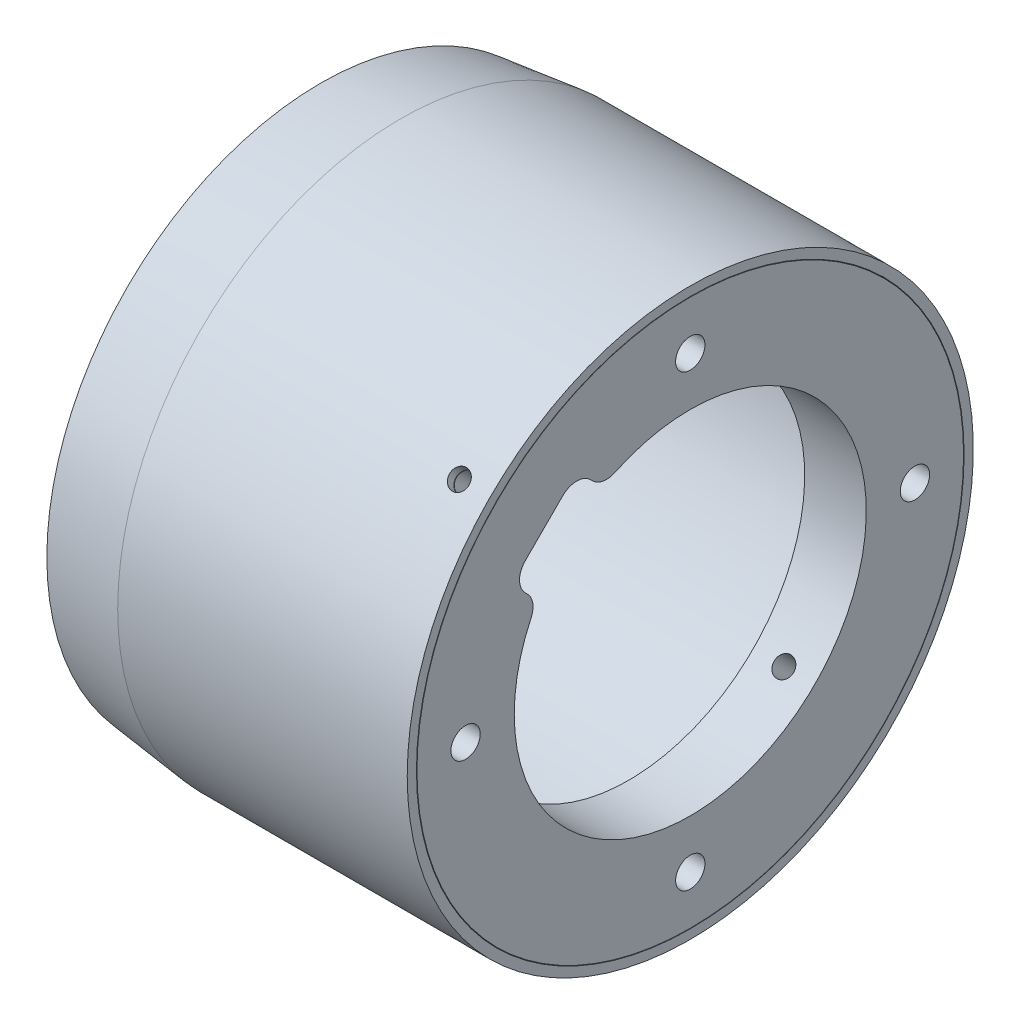
SolidWorks part; units mm, degrees
material "6061 Alloy"
ref_plane "Front Plane" through (0, 0, 0) normal (0, 0, 1) x (1, 0, 0)
ref_plane "Top Plane" through (0, 0, 0) normal (0, 1, 0) x (1, 0, 0)
ref_plane "Right Plane" through (0, 0, 0) normal (1, 0, 0) x (0, 0, -1)
sketch "Sketch1" plane through (0, 0, 0) normal (0, 0, 1) x (1, 0, 0)
  line L0 (0, 0) -> (74.8253, 0) construction
  line L1 (13, 45.95) -> (60, 45.95)
  line L5 (60, 44.45) -> (0, 44.45)
  line L6 (0, 44.45) -> (13, 45.95)
  line L7 (0, 0) -> (0, 44.45) construction
  line L17 (60, 44.45) -> (60, 45.95)
  dimension "D1" = 88.9
  dimension "D2" = 60
  dimension "D3" = 13
  dimension "D6" = 1.5
revolve "Revolve1" add sketch "Sketch1" angle 360 about L0
sketch "Sketch2" plane through (0, 0, 0) normal (0, 0, 1) x (1, 0, 0)
  line L0 (0, 0) -> (60, 0) construction
  line L2 (60, -45.95) -> (60, 45.95) construction
  line L3 (60, 44.37) -> (50, 44.37)
  line L4 (60, 44.37) -> (60, 28.575)
  line L5 (60, 28.575) -> (50, 28.575)
  line L6 (50, 44.37) -> (50, 28.575)
  line L7 (60, -45.95) -> (60, 45.95) construction
  line L8 (60, 44.45) -> (0, 44.45) construction
  dimension "D1" = 10
  dimension "D2" = 28.575
  dimension "D3" = 0.08
revolve "Revolve2" add sketch "Sketch2" angle 360 about L0
sketch "Sketch3" plane through (60, 0, 0) normal (1, 0, 0) x (0, 0, -1)
  line L0 (-36.4725, 0) -> (0, 0) construction
  line L1 (0, 36.4725) -> (0, 0) construction
  line L2 (36.4725, 0) -> (0, 0) construction
  line L3 (0, -36.4725) -> (0, 0) construction
  line L4 (-28.575, 0) -> (-44.37, 0) construction
  circle A0 centre (-36.4725, 0) radius 2.3812
  circle A1 centre (0, 36.4725) radius 2.3812
  circle A2 centre (36.4725, 0) radius 2.3812
  circle A3 centre (0, -36.4725) radius 2.3812
  circle A4 centre (0, 0) radius 28.575 construction
  circle A5 centre (0, 0) radius 44.37 construction
  point P13 (0, 0)
  point P17 (0, 0)
  dimension "D1" = 4.7625
  dimension "D3" = 4
extrude "Cut-Extrude1" cut sketch "Sketch3" against normal through all
ref_plane "Plane1" through (0, 32.4916, 32.4916) normal (0, 0.7071, 0.7071) x (-1, 0, 0)
sketch "Sketch4" plane through (0, 32.4916, 32.4916) normal (0, 0.7071, 0.7071) x (-1, 0, 0)
  line L0 (-55, 0) -> (0, 0) construction
  line L1 (-60, 45.95) -> (-60, -45.95) construction
  circle A0 centre (-55, 0) radius 1.5875
  dimension "D1" = 3.175
  dimension "D2" = 5
extrude "Cut-Extrude2" cut sketch "Sketch4" against normal up to surface (17.4191 mm away)
ref_axis "Axis1" through (60, 0, 0) along (-1, 0, 0)
pattern_circular "CirPattern1" count 4 over 360 about axis through (60, 0, 0) along (-1, 0, 0) of "Cut-Extrude2"
sketch "Sketch5" plane through (60, 0, 0) normal (1, 0, 0) x (0, 0, -1)
  line L0 (0, 0) -> (-20.2056, 20.2056) construction
  line L3 (0, 0) -> (0, 36.4725) construction
  line L5 (-21.9733, 11.3667) -> (-18.4378, 29.0444) construction
  line L6 (-29.0444, 18.4378) -> (-11.3667, 21.9733) construction
  line L7 (-29.0444, 18.4378) -> (-18.4378, 29.0444)
  line L8 (-18.4378, 29.0444) -> (-11.3667, 21.9733)
  line L9 (-11.3667, 21.9733) -> (-21.9733, 11.3667)
  line L10 (-21.9733, 11.3667) -> (-29.0444, 18.4378)
  circle A0 centre (0, 0) radius 28.575 construction
  point P10 (-20.2056, 20.2056)
  point P12 (-20.2056, 20.2056)
  point P13 (-21.61, 15.2149)
  dimension "D1" = 45
  dimension "D2" = 15
  dimension "D3" = 10
extrude "Cut-Extrude3" cut sketch "Sketch5" against normal up to surface (10 mm away) up to face at (50, 0, 34.0913)
fillet "Fillet1" radius 3.2 4 edges at (55, 14.1939, 24.8005) (55, 24.8005, 14.1939) (55, 18.4378, 29.0444) (55, 29.0444, 18.4378)
